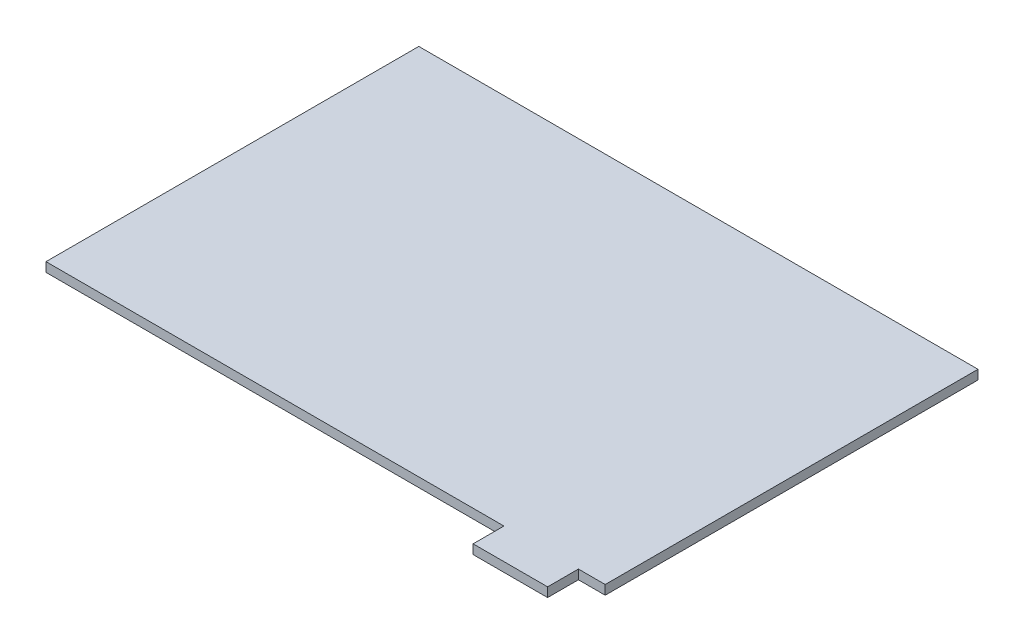
SolidWorks part; units mm, degrees
ref_plane "Front Plane" through (0, 0, 0) normal (0, 0, 1) x (1, 0, 0)
ref_plane "Top Plane" through (0, 0, 0) normal (0, 1, 0) x (1, 0, 0)
ref_plane "Right Plane" through (0, 0, 0) normal (1, 0, 0) x (0, 0, -1)
sketch "Sketch1" plane through (0, 0, 0) normal (0, 1, 0) x (1, 0, 0)
  line L0 (48.6, -50.8) -> (48.6, -59.2)
  line L1 (-76.2, -50.8) -> (48.6, -50.8)
  line L2 (-76.2, -50.8) -> (-76.2, 50.8)
  line L3 (-76.2, 50.8) -> (76.2, 50.8)
  line L4 (76.2, -50.8) -> (76.2, 50.8)
  line L5 (-76.2, -50.8) -> (76.2, 50.8) construction
  line L6 (-76.2, 50.8) -> (76.2, -50.8) construction
  line L7 (48.6, -59.2) -> (68.9, -59.2)
  line L8 (68.9, -59.2) -> (68.9, -50.8)
  line L9 (68.9, -50.8) -> (76.2, -50.8)
  point P0 (0, 0)
  point P5 (68.9, -50.8)
  point P6 (48.6, -50.8)
  dimension "D1" = 152.4
  dimension "D2" = 101.6
  dimension "D3" = 7.3
  dimension "D4" = 124.8
  dimension "D5" = 8.4
extrude "Boss-Extrude1" add sketch "Sketch1" along normal blind 2.54
